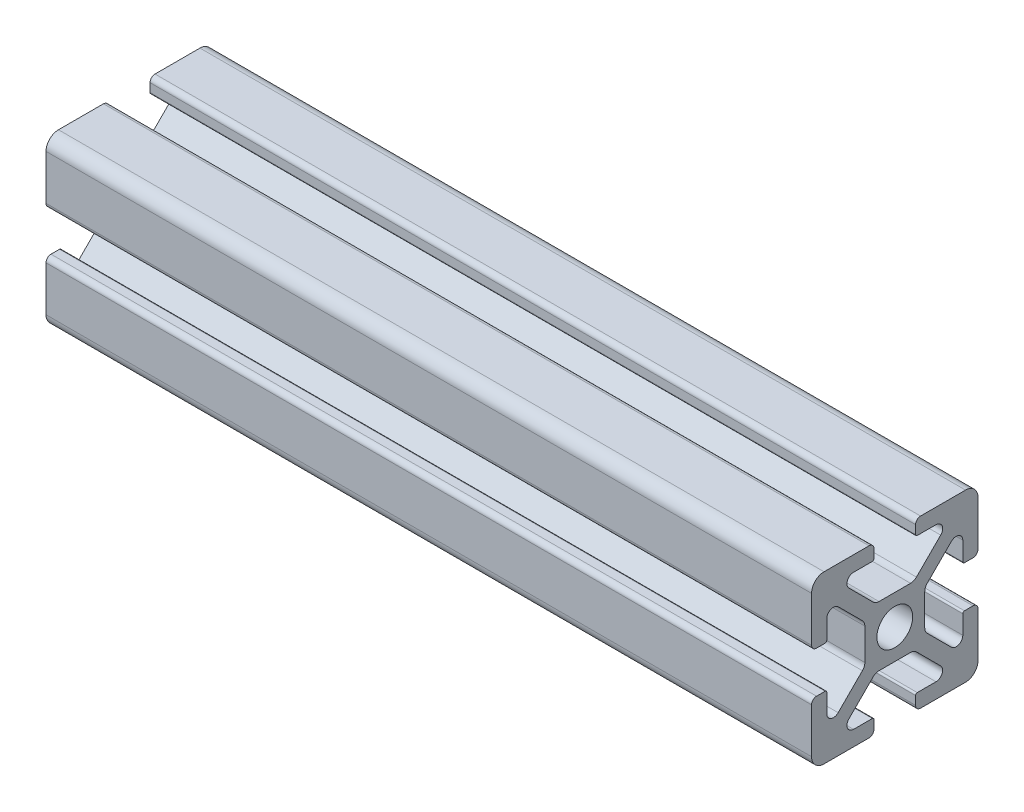
SolidWorks part; units mm, degrees
ref_plane "Front Plane" through (0, 0, 0) normal (0, 0, 1) x (1, 0, 0)
ref_plane "Top Plane" through (0, 0, 0) normal (0, 1, 0) x (1, 0, 0)
ref_plane "Right Plane" through (0, 0, 0) normal (1, 0, 0) x (0, 0, -1)
sketch "Sketch1" plane through (0, 0, 0) normal (1, 0, 0) x (0, 0, -1)
  line L0 (0, -10) -> (0, 10) construction
  line L1 (10, -10) -> (-10, -10)
  line L2 (10, -10) -> (10, 10)
  line L3 (10, 10) -> (0, 10)
  line L4 (-10, -10) -> (-10, 10)
  line L5 (10, -10) -> (-10, 10) construction
  line L6 (10, 10) -> (-10, -10) construction
  line L7 (10, 0) -> (-10, 0) construction
  line L8 (-2.5, 9.4) -> (-2.5, 8.3731)
  line L9 (-2.7, 8.1731) -> (-4.95, 8.1731)
  line L10 (-5.5157, 6.8075) -> (-2.6011, 3.8929)
  line L11 (-1.894, 3.6) -> (0, 3.6)
  line L12 (-5.3502, 4.0584) -> (-4.0584, 5.3502) construction
  line L13 (-3.825, 8.1731) -> (-3.825, 10) construction
  line L14 (-3.1, 10) -> (-10, 10)
  line L15 (-5.75, 7.3731) -> (5.75, 7.3731) construction
  circle A0 centre (0, 0) radius 2.15
  arc A1 (-4.95, 8.1731) -> (-5.5157, 6.8075) centre (-4.95, 7.3731) ccw
  arc A2 (-2.6011, 3.8929) -> (-1.894, 3.6) centre (-1.894, 4.6) ccw
  arc A3 (-2.5, 8.3731) -> (-2.7, 8.1731) centre (-2.7, 8.3731) cw
  arc A4 (-2.5, 9.4) -> (-3.1, 10) centre (-3.1, 9.4) ccw
  point P0 (0, 0)
  point P9 (0, 0)
  point P12 (0, 0)
  point P22 (-4.7043, 4.7043)
  point P32 (-2.5, 10)
  point P33 (-2.5, 8.8866)
  point P35 (-4.0584, 5.3502)
  point P37 (0, 7.3731)
  dimension "Center Hole Diameter" = 4.3
  dimension "D4" = 1
  dimension "D5" = 0.2
  dimension "D6" = 0.6
  dimension "D3" = 0.8
  dimension "Rail Height" = 20
  dimension "D7" = 6.4
  dimension "T Slot Width" = 5
  dimension "D10" = 10
  dimension "Rail Width" = 20
  dimension "D2" = 11.5
sketch "Sketch2" plane through (0, 0, 0) normal (0, 0, 1) x (1, 0, 0)
  line L0 (-132.4, 10) -> (-132.4, -10) construction
  line L1 (152.4, -10) -> (-152.4, -10) construction
  line L2 (152.4, -10) -> (152.4, 10) construction
  line L3 (152.4, 10) -> (-152.4, 10) construction
  line L4 (-152.4, -10) -> (-152.4, 10) construction
  line L5 (152.4, -10) -> (-152.4, 10) construction
  line L6 (152.4, 10) -> (-152.4, -10) construction
  line L7 (132.4, 10) -> (132.4, -10) construction
  point P0 (0, 0)
  point P12 (132.4, 0)
  dimension "Length" = 304.8
  dimension "D1" = 20
  dimension "D2" = 20
sketch "Sketch3" plane through (0, 0, 0) normal (1, 0, 0) x (0, 0, -1)
  line L0 (-5.5157, 6.8075) -> (-2.6011, 3.8929) construction
  line L5 (-3.1, 10) -> (-10, 10) construction
  line L6 (-2.5, 9.4) -> (-2.5, 8.3731) construction
  line L7 (-2.7, 8.1731) -> (-4.95, 8.1731) construction
  line L8 (-1.894, 3.6) -> (0, 3.6) construction
  line L9 (-5.5157, 6.8075) -> (-2.6011, 3.8929)
  line L10 (-10, 10) -> (0, 0) construction
  line L12 (-3.6, 1.894) -> (-3.6, 0)
  line L13 (-8.1731, 2.7) -> (-8.1731, 4.95)
  line L14 (-3.1, 10) -> (-8.5, 10)
  line L15 (-2.5, 9.4) -> (-2.5, 8.3731)
  line L16 (-2.7, 8.1731) -> (-4.95, 8.1731)
  line L17 (-1.894, 3.6) -> (0, 3.6)
  line L18 (-9.4, 2.5) -> (-8.3731, 2.5)
  line L19 (-10, 3.1) -> (-10, 8.5)
  line L20 (-6.8075, 5.5157) -> (-3.8929, 2.6011)
  line L21 (-3.6, 0) -> (-2.15, 0)
  line L22 (0, 3.6) -> (0, 2.15)
  arc A0 (-2.5, 9.4) -> (-3.1, 10) centre (-3.1, 9.4) ccw construction
  arc A1 (-2.7, 8.1731) -> (-2.5, 8.3731) centre (-2.7, 8.3731) ccw construction
  arc A2 (-4.95, 8.1731) -> (-5.5157, 6.8075) centre (-4.95, 7.3731) ccw construction
  arc A3 (-2.6011, 3.8929) -> (-1.894, 3.6) centre (-1.894, 4.6) ccw construction
  arc A4 (-2.5, 9.4) -> (-3.1, 10) centre (-3.1, 9.4) ccw
  arc A5 (-2.7, 8.1731) -> (-2.5, 8.3731) centre (-2.7, 8.3731) ccw
  arc A6 (-4.95, 8.1731) -> (-5.5157, 6.8075) centre (-4.95, 7.3731) ccw
  arc A7 (-2.6011, 3.8929) -> (-1.894, 3.6) centre (-1.894, 4.6) ccw
  arc A8 (-3.8929, 2.6011) -> (-3.6, 1.894) centre (-4.6, 1.894) cw
  arc A9 (-8.1731, 4.95) -> (-6.8075, 5.5157) centre (-7.3731, 4.95) cw
  arc A10 (-8.1731, 2.7) -> (-8.3731, 2.5) centre (-8.3731, 2.7) cw
  arc A11 (-9.4, 2.5) -> (-10, 3.1) centre (-9.4, 3.1) cw
  circle A12 centre (0, 0) radius 2.15 construction
  arc A13 (0, 2.15) -> (-2.15, 0) centre (0, 0) ccw
  arc A14 (-10, 8.5) -> (-8.5, 10) centre (-8.5, 8.5) cw
  dimension "D1" = 1.5
extrude "Boss-Extrude1" add sketch "Sketch3" against normal blind 92
mirror "Mirror1" about plane through (0, 0, 0) normal (0, 1, 0) of bodies 104
mirror "Mirror2" about plane through (0, 0, 0) normal (0, 0, 1) of bodies 105
equation "\"D10@Sketch1\" = \"Rail Height@Sketch1\" / 2"
equation "\"D2@Sketch2\"=\"D1@Sketch2\""
